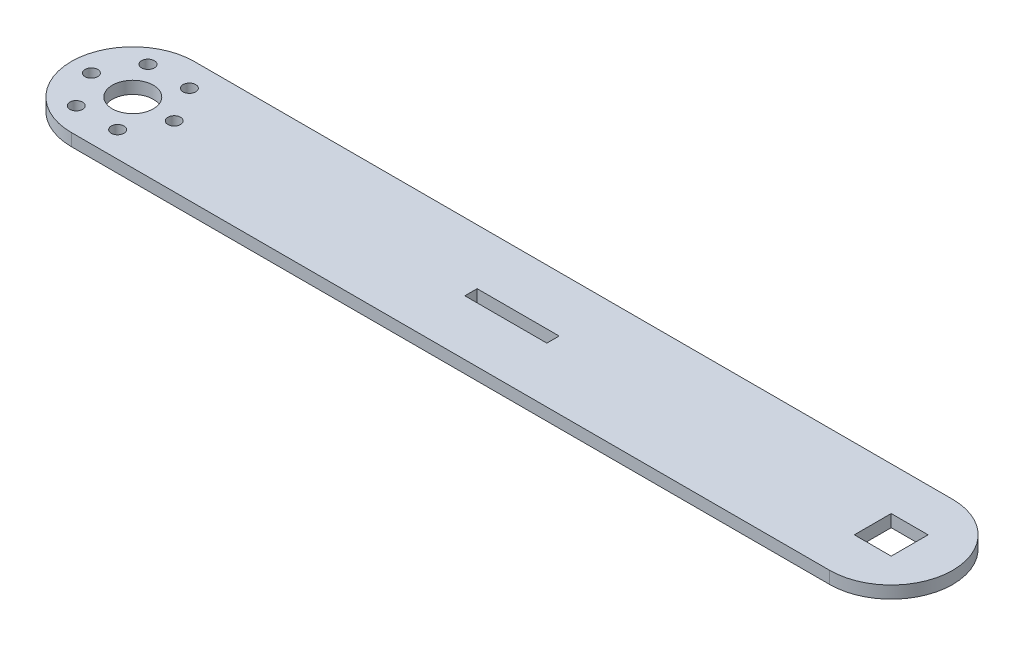
SolidWorks part; units mm, degrees
ref_plane "Front Plane" through (0, 0, 0) normal (0, 0, 1) x (1, 0, 0)
ref_plane "Top Plane" through (0, 0, 0) normal (0, 1, 0) x (1, 0, 0)
ref_plane "Right Plane" through (0, 0, 0) normal (1, 0, 0) x (0, 0, -1)
sketch "Sketch1" plane through (0, 0, 0) normal (0, 1, 0) x (1, 0, 0)
  line L0 (0, 15) -> (185, 15)
  line L1 (0, -15) -> (185, -15)
  line L3 (82.5, -1.5) -> (102.5, -1.5)
  line L4 (82.5, -1.5) -> (82.5, 1.5)
  line L5 (82.5, 1.5) -> (102.5, 1.5)
  line L6 (102.5, -1.5) -> (102.5, 1.5)
  line L7 (82.5, -1.5) -> (102.5, 1.5) construction
  line L8 (82.5, 1.5) -> (102.5, -1.5) construction
  line L9 (189.5, -4.5) -> (180.5, -4.5)
  line L10 (189.5, -4.5) -> (189.5, 4.5)
  line L11 (189.5, 4.5) -> (180.5, 4.5)
  line L12 (180.5, -4.5) -> (180.5, 4.5)
  line L13 (189.5, -4.5) -> (180.5, 4.5) construction
  line L14 (189.5, 4.5) -> (180.5, -4.5) construction
  line L15 (10.1036, 0) -> (5.0518, 8.75) construction
  line L16 (5.0518, 8.75) -> (-5.0518, 8.75) construction
  line L17 (-5.0518, 8.75) -> (-10.1036, 0) construction
  line L18 (-10.1036, 0) -> (-5.0518, -8.75) construction
  line L19 (-5.0518, -8.75) -> (5.0518, -8.75) construction
  line L20 (5.0518, -8.75) -> (10.1036, 0) construction
  arc A0 (0, -15) -> (0, 15) centre (0, 0) cw
  arc A1 (185, -15) -> (185, 15) centre (185, 0) ccw
  circle A2 centre (0, 0) radius 5
  circle A5 centre (0, 0) radius 5
  circle A7 centre (0, 0) radius 5
  circle A9 centre (0, 0) radius 5
  circle A11 centre (0, 0) radius 5
  circle A13 centre (0, 0) radius 5
  circle A19 centre (0, 0) radius 8.75 construction
  circle A23 centre (5.0518, 8.75) radius 1.55
  circle A24 centre (10.1036, 0) radius 1.55
  circle A25 centre (5.0518, -8.75) radius 1.55
  circle A26 centre (-5.0518, -8.75) radius 1.55
  circle A27 centre (-10.1036, 0) radius 1.55
  circle A28 centre (-5.0518, 8.75) radius 1.55
  point P7 (92.5, 0)
  point P14 (92.5, 15)
  point P27 (0, 0)
  point P28 (0, 0)
  point P30 (0, 0)
  point P31 (0, 0)
  dimension "D2" = 15
  dimension "D3" = 15
  dimension "D4" = 10
  dimension "D8" = 17.5
  dimension "D10" = 3.1
  dimension "D1" = 185
  dimension "D5" = 3
  dimension "D6" = 20
  dimension "D7" = 9
  dimension "D9" = 6
extrude "Boss-Extrude1" add sketch "Sketch1" along normal mid plane 3
